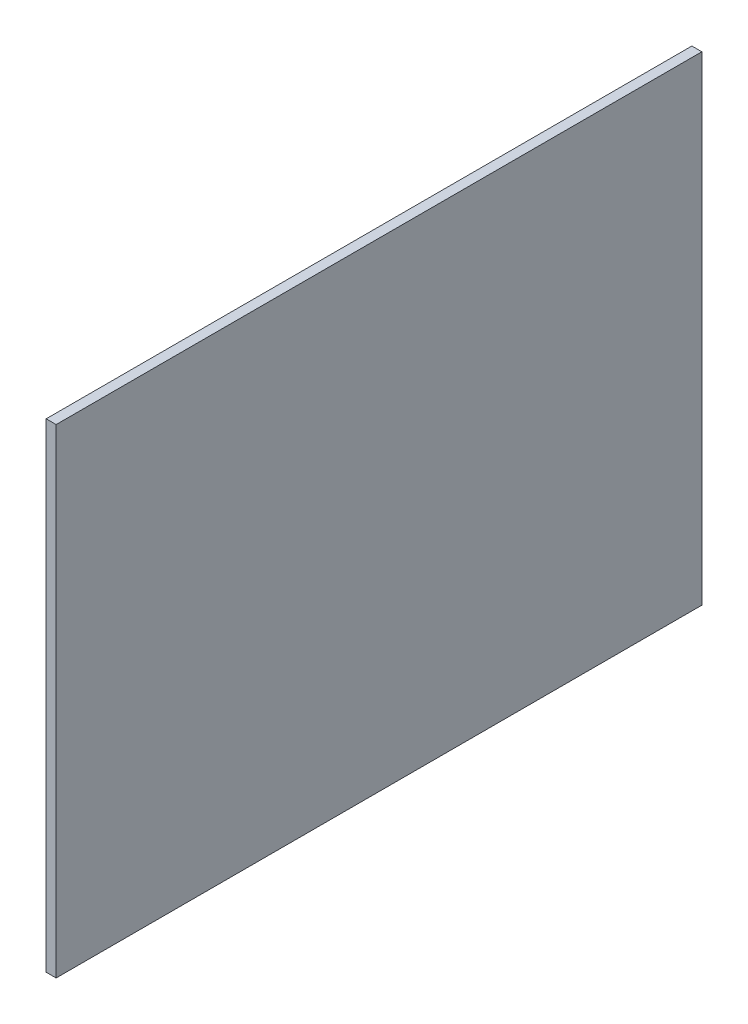
SolidWorks part; units mm, degrees
ref_plane "Front Plane" through (0, 0, 0) normal (0, 0, 1) x (1, 0, 0)
ref_plane "Top Plane" through (0, 0, 0) normal (0, 1, 0) x (1, 0, 0)
ref_plane "Right Plane" through (0, 0, 0) normal (1, 0, 0) x (0, 0, -1)
sketch "Sketch1" plane through (0, 0, 0) normal (1, 0, 0) x (0, 0, -1)
  line L1 (-97, 72) -> (97, 72)
  line L2 (-97, 72) -> (-97, -72)
  line L3 (-97, -72) -> (97, -72)
  line L4 (97, 72) -> (97, -72)
  point P4 (0, -72)
  point P6 (-97, 0)
  dimension "D1" = 194
  dimension "D2" = 144
extrude "Boss-Extrude1" add sketch "Sketch1" along normal blind 3
